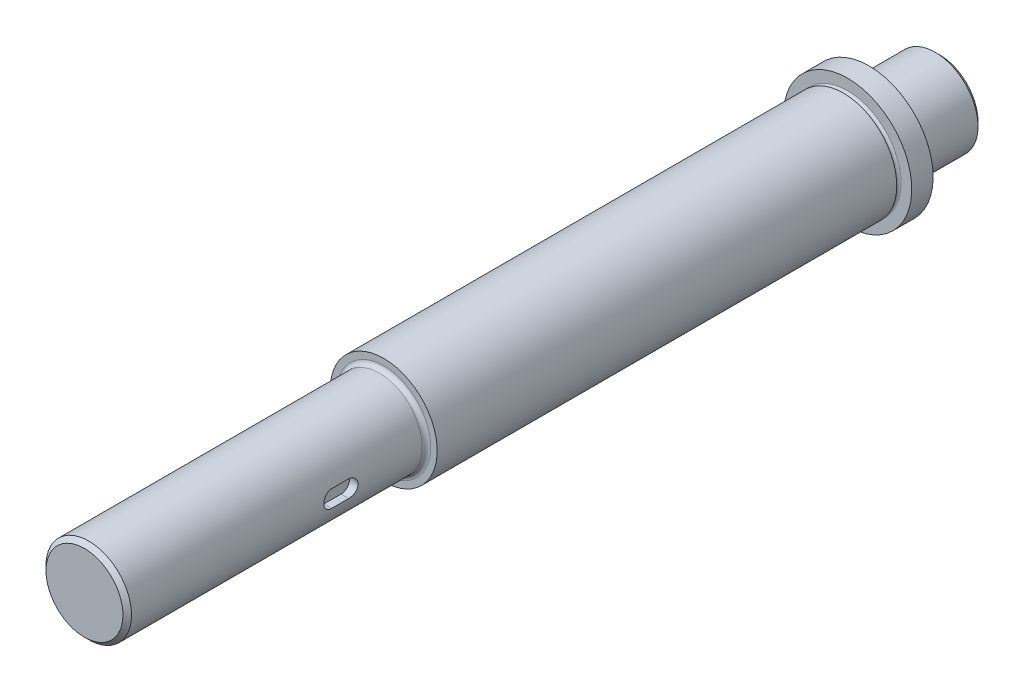
SolidWorks part; units mm, degrees
material "AISI 1045 Steel, cold drawn"
ref_plane "Front Plane" through (0, 0, 0) normal (0, 0, 1) x (1, 0, 0)
ref_plane "Top Plane" through (0, 0, 0) normal (0, 1, 0) x (1, 0, 0)
ref_plane "Right Plane" through (0, 0, 0) normal (1, 0, 0) x (0, 0, -1)
sketch "Sketch1" plane through (0, 0, 0) normal (1, 0, 0) x (0, 0, -1)
  line L0 (0, 0) -> (-200, 0) construction
  line L1 (0, 0) -> (0, -10)
  line L2 (-21.5, -12.5) -> (-21.5, -15)
  line L4 (-22.5, -12.5) -> (-130, -12.5)
  line L9 (-130, -12.5) -> (-130, -10)
  line L10 (-130, -10) -> (-200, -10)
  line L11 (-200, -10) -> (-200, 0)
  line L12 (0, 0) -> (-200, 0)
  line L13 (-21.5, -15) -> (-16.5, -15)
  line L14 (-16.5, -15) -> (-16.5, -10)
  line L15 (-16.5, -10) -> (0, -10)
  arc A0 (-21.5, -12.5) -> (-22.5, -12.5) centre (-22, -12.5) ccw
  dimension "D9" = 1
  dimension "D1" = 10
  dimension "D2" = 107.5
  dimension "D3" = 12.5
  dimension "D5" = 200
  dimension "D6" = 70
  dimension "D10" = 10
  dimension "D11" = 10
  dimension "D12" = 5
  dimension "D13" = 15
revolve "Revolve1" add sketch "Sketch1" angle 360 about L0
cosmetic thread "Cosmetic Thread1" parameters "D1"=15, "D2"=17.252
fillet "Fillet1" radius 1 1 edges at (0, 10, 130)
fillet "Fillet2" radius 3 1 edges at (0, 10, 16.5)
chamfer "Chamfer1" distance 1 angle 45 1 edges at (0, 10, 200)
sketch "Sketch2" plane through (0, 0, 0) normal (1, 0, 0) x (0, 0, -1)
  line L0 (-148, 0) -> (-152, 0) construction
  line L1 (-148, -2) -> (-152, -2)
  line L2 (-148, 2) -> (-152, 2)
  line L3 (-200, 9) -> (-200, -9) construction
  arc A0 (-148, -2) -> (-148, 2) centre (-148, 0) ccw
  arc A1 (-152, 2) -> (-152, -2) centre (-152, 0) ccw
  point P3 (-150, 0)
  dimension "D2" = 2
  dimension "D1" = 4
  dimension "D3" = 50
extrude "Cut-Extrude2" cut sketch "Sketch2" against normal blind 2 from offset 10
chamfer "Chamfer2" distance 1 angle 45 1 edges at (0, 10, 0)
